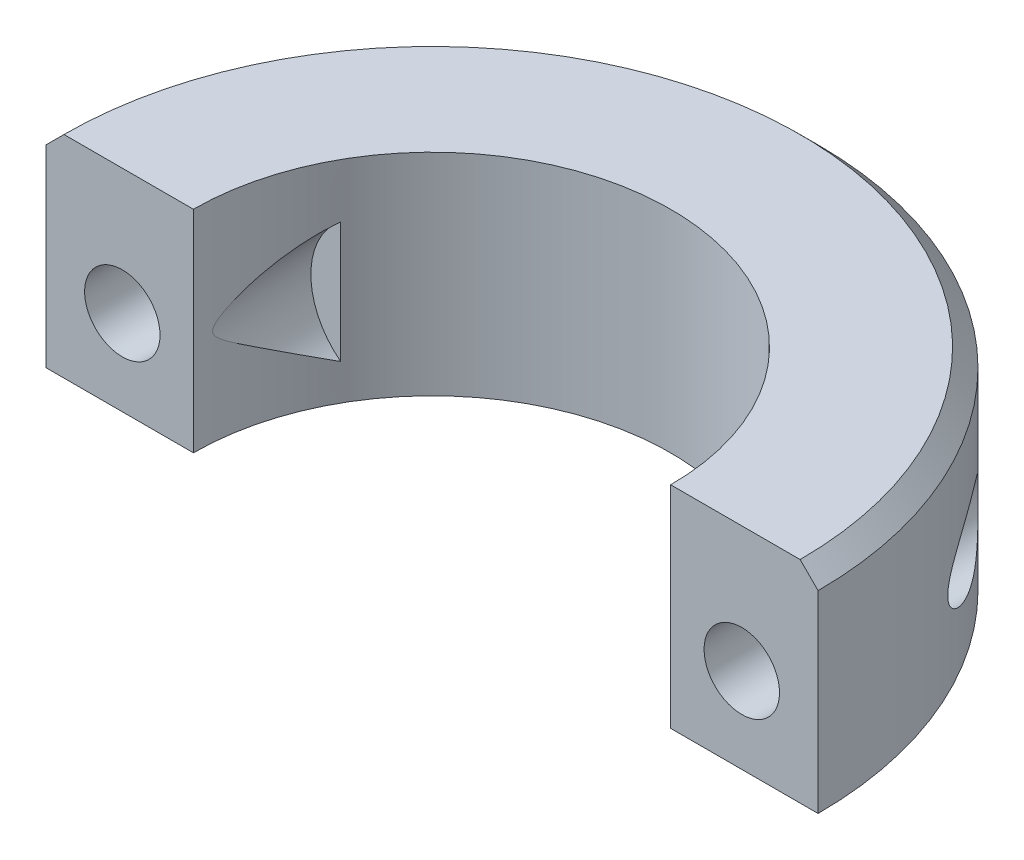
SolidWorks part; units mm, degrees
ref_plane "Front Plane" through (0, 0, 0) normal (0, 0, 1) x (1, 0, 0)
ref_plane "Top Plane" through (0, 0, 0) normal (0, 1, 0) x (1, 0, 0)
ref_plane "Right Plane" through (0, 0, 0) normal (1, 0, 0) x (0, 0, -1)
sketch "Sketch1" plane through (0, 0, 0) normal (0, 1, 0) x (1, 0, 0)
  line L0 (-21.5, 0) -> (-13.29, 0)
  line L1 (13.29, 0) -> (21.5, 0)
  arc A0 (21.5, 0) -> (-21.5, 0) centre (0, 0) ccw
  arc A1 (13.29, 0) -> (-13.29, 0) centre (0, 0) ccw
  dimension "D1" = 43
  dimension "D2" = 26.58
extrude "Boss-Extrude1" add sketch "Sketch1" along normal mid plane 11.75
chamfer "Chamfer1" distance 1 angle 45 1 edges at (0, 5.875, -21.5)
sketch "Sketch2" plane through (0, 0, 0) normal (0, 0, 1) x (1, 0, 0)
  line L0 (0, 0) -> (0, 18.7661) construction
  line L1 (-20.5, 5.875) -> (-13.29, 5.875) construction
  line L2 (-21.5, -0.5) -> (21.5, -0.5) construction
  line L3 (-21.5, 4.875) -> (-21.5, -5.875) construction
  line L4 (21.5, 4.875) -> (21.5, -5.875) construction
  circle A0 centre (-17.25, -1.125) radius 2.1
  circle A1 centre (17.25, -1.125) radius 2.1
  dimension "D2" = 4.2
  dimension "D1" = 7
  dimension "D3" = 34.5
extrude "Cut-Extrude1" cut sketch "Sketch2" against normal through all
sketch "Sketch3" plane through (0, 0, 0) normal (0, 0, 1) x (1, 0, 0)
  line L0 (-21.5, -0.5) -> (21.5, -0.5) construction
  line L1 (-21.5, 4.875) -> (-21.5, -5.875) construction
  line L2 (21.5, 4.875) -> (21.5, -5.875) construction
  line L3 (0, 0) -> (0, 15.8689) construction
  circle A0 centre (-9, -0.5) radius 4.25
  circle A1 centre (9, -0.5) radius 4.25
  dimension "D1" = 8.5
  dimension "D2" = 18
extrude "Cut-Extrude2" cut sketch "Sketch3" against normal blind 6.5
